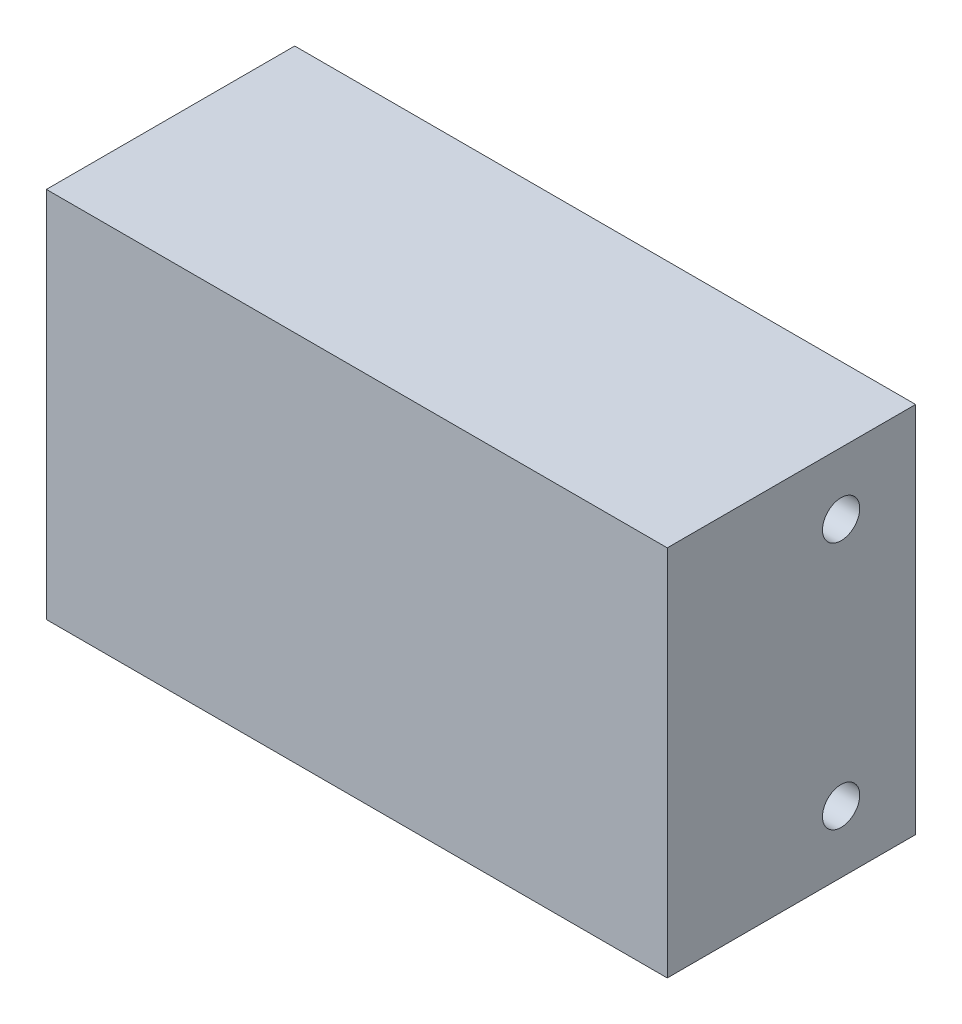
SolidWorks part; units mm, degrees
material "PP Copolymer"
ref_plane "Front Plane" through (0, 0, 0) normal (0, 0, 1) x (1, 0, 0)
ref_plane "Top Plane" through (0, 0, 0) normal (0, 1, 0) x (1, 0, 0)
ref_plane "Right Plane" through (0, 0, 0) normal (1, 0, 0) x (0, 0, -1)
sketch "Sketch1" plane through (0, 0, 0) normal (0, 1, 0) x (1, 0, 0)
  line L1 (0, 0) -> (25, 0)
  line L2 (0, 0) -> (0, 10)
  line L3 (0, 10) -> (25, 10)
  line L4 (25, 0) -> (25, 10)
  dimension "D1" = 25
  dimension "D2" = 10
extrude "Boss-Extrude1" add sketch "Sketch1" along normal blind 15
sketch "Sketch2" plane through (0, 0, 0) normal (0, -1, 0) x (1, 0, 0)
  line L0 (12.5, 0) -> (12.5, -4) construction
  line L1 (0, 0) -> (25, 0) construction
  line L2 (12.5, -4) -> (17.5, -4) construction
  line L3 (12.5, -4) -> (7.5, -4) construction
  circle A0 centre (7.5, -4) radius 0.75
  circle A1 centre (17.5, -4) radius 0.75
  dimension "D3" = 1.5
  dimension "D1" = 5
  dimension "D2" = 4
extrude "Cut-Extrude1" cut sketch "Sketch2" against normal blind 10
sketch "Sketch3" plane through (0, 0, 0) normal (-1, 0, 0) x (0, 0, 1)
  line L0 (-10, 7.5) -> (-7, 7.5) construction
  line L1 (-10, 15) -> (-10, 0) construction
  line L2 (-7, 7.5) -> (-7, 10.5) construction
  line L3 (-7, 7.5) -> (-7, 4.5) construction
  circle A0 centre (-7, 10.5) radius 0.75
  circle A1 centre (-7, 4.5) radius 0.75
  dimension "D2" = 1.5
  dimension "D1" = 3
  dimension "D3" = 3
extrude "Cut-Extrude2" cut sketch "Sketch3" against normal blind 10
sketch "Sketch4" plane through (25, 0, 0) normal (1, 0, 0) x (0, 0, -1)
  line L0 (10, 7.5) -> (7, 7.5) construction
  line L1 (10, 15) -> (10, 0) construction
  line L2 (7, 7.5) -> (7, 12.5) construction
  line L3 (7, 7.5) -> (7, 2.5) construction
  circle A0 centre (7, 12.5) radius 0.75
  circle A1 centre (7, 2.5) radius 0.75
  dimension "D3" = 1.5
  dimension "D1" = 3
  dimension "D2" = 5
extrude "Cut-Extrude3" cut sketch "Sketch4" against normal blind 10
